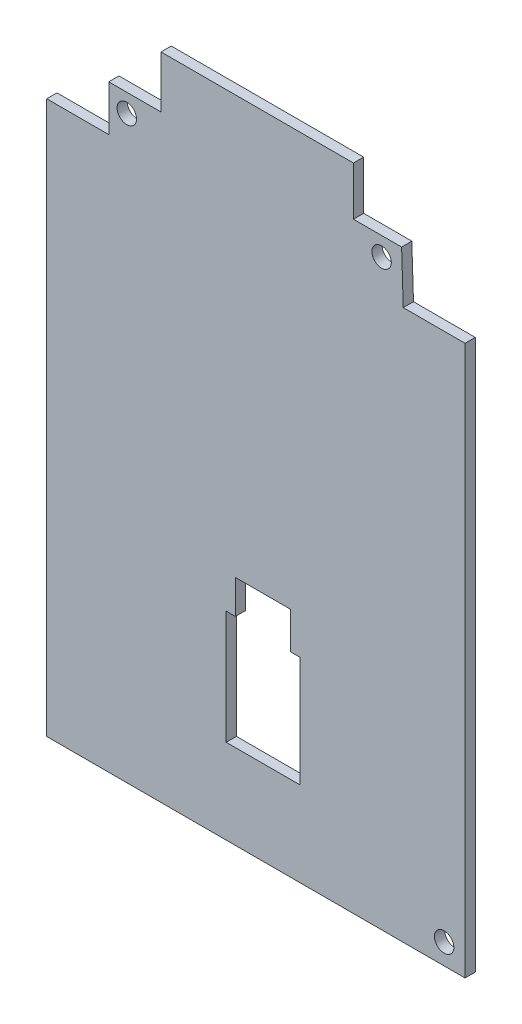
SolidWorks part; units mm, degrees
material "Petg 30% Infill"
ref_plane "Front Plane" through (0, 0, 0) normal (0, 0, 1) x (1, 0, 0)
ref_plane "Top Plane" through (0, 0, 0) normal (0, 1, 0) x (1, 0, 0)
ref_plane "Right Plane" through (0, 0, 0) normal (1, 0, 0) x (0, 0, -1)
sketch "Sketch6" plane through (0, 0, 0) normal (0, 0, 1) x (1, 0, 0)
  line L0 (501.7385, 124.7244) -> (807.8803, 124.7244)
  line L1 (807.8803, 124.7244) -> (807.8803, 34.0157)
  line L2 (807.8803, 34.0157) -> (501.7385, 34.0157)
  line L3 (501.7385, 34.0157) -> (501.7385, 124.7244)
  line L4 (28.3465, 566.9496) -> (813.5496, 566.9496)
  line L5 (813.5496, 566.9496) -> (813.5496, 28.3465)
  line L6 (813.5496, 28.3465) -> (28.3465, 28.3465)
  line L7 (28.3465, 28.3465) -> (28.3465, 566.9496)
  line L8 (34.0157, 561.2803) -> (807.8803, 561.2803)
  line L9 (807.8803, 561.2803) -> (807.8803, 34.0157)
  line L10 (807.8803, 34.0157) -> (34.0157, 34.0157)
  line L11 (34.0157, 34.0157) -> (34.0157, 561.2803)
  line L12 (170.0787, 561.2803) -> (170.0787, 566.9496)
  line L13 (311.811, 561.2803) -> (311.811, 566.9496)
  line L14 (453.5433, 561.2803) -> (453.5433, 566.9496)
  line L15 (595.2756, 561.2803) -> (595.2756, 566.9496)
  line L16 (737.0079, 561.2803) -> (737.0079, 566.9496)
  line L17 (102.3001, 562.4323) -> (100.1942, 562.4323)
  line L18 (101.247, 562.4323) -> (101.247, 566.1173)
  line L19 (101.247, 566.1173) -> (100.8961, 565.5909)
  line L20 (100.8961, 565.5909) -> (100.5452, 565.24)
  line L21 (100.5452, 565.24) -> (100.1942, 565.0645)
  line L22 (241.9265, 565.7664) -> (242.102, 565.9418)
  line L23 (242.102, 565.9418) -> (242.4529, 566.1173)
  line L24 (242.4529, 566.1173) -> (243.3302, 566.1173)
  line L25 (243.3302, 566.1173) -> (243.6815, 565.9418)
  line L26 (243.6815, 565.9418) -> (243.8569, 565.7664)
  line L27 (243.8569, 565.7664) -> (244.0324, 565.4155)
  line L28 (244.0324, 565.4155) -> (244.0324, 565.0645)
  line L29 (244.0324, 565.0645) -> (243.8569, 564.5381)
  line L30 (243.8569, 564.5381) -> (241.7511, 562.4323)
  line L31 (241.7511, 562.4323) -> (244.0324, 562.4323)
  line L32 (383.4833, 566.1173) -> (385.7647, 566.1173)
  line L33 (385.7647, 566.1173) -> (384.5362, 564.7136)
  line L34 (384.5362, 564.7136) -> (385.0626, 564.7136)
  line L35 (385.0626, 564.7136) -> (385.4137, 564.5381)
  line L36 (385.4137, 564.5381) -> (385.5892, 564.3624)
  line L37 (385.5892, 564.3624) -> (385.7647, 564.0115)
  line L38 (385.7647, 564.0115) -> (385.7647, 563.1341)
  line L39 (385.7647, 563.1341) -> (385.5892, 562.7832)
  line L40 (385.5892, 562.7832) -> (385.4137, 562.6077)
  line L41 (385.4137, 562.6077) -> (385.0626, 562.4323)
  line L42 (385.0626, 562.4323) -> (384.0097, 562.4323)
  line L43 (384.0097, 562.4323) -> (383.6588, 562.6077)
  line L44 (383.6588, 562.6077) -> (383.4833, 562.7832)
  line L45 (527.146, 564.8891) -> (527.146, 562.4323)
  line L46 (526.2684, 566.2928) -> (525.3911, 563.6605)
  line L47 (525.3911, 563.6605) -> (527.6724, 563.6605)
  line L48 (669.0538, 566.1173) -> (667.2989, 566.1173)
  line L49 (667.2989, 566.1173) -> (667.1234, 564.3624)
  line L50 (667.1234, 564.3624) -> (667.2989, 564.5381)
  line L51 (667.2989, 564.5381) -> (667.6498, 564.7136)
  line L52 (667.6498, 564.7136) -> (668.5271, 564.7136)
  line L53 (668.5271, 564.7136) -> (668.8783, 564.5381)
  line L54 (668.8783, 564.5381) -> (669.0538, 564.3624)
  line L55 (669.0538, 564.3624) -> (669.2293, 564.0115)
  line L56 (669.2293, 564.0115) -> (669.2293, 563.1341)
  line L57 (669.2293, 563.1341) -> (669.0538, 562.7832)
  line L58 (669.0538, 562.7832) -> (668.8783, 562.6077)
  line L59 (668.8783, 562.6077) -> (668.5271, 562.4323)
  line L60 (668.5271, 562.4323) -> (667.6498, 562.4323)
  line L61 (667.6498, 562.4323) -> (667.2989, 562.6077)
  line L62 (667.2989, 562.6077) -> (667.1234, 562.7832)
  line L63 (810.6106, 566.1173) -> (809.9085, 566.1173)
  line L64 (809.9085, 566.1173) -> (809.5575, 565.9418)
  line L65 (809.5575, 565.9418) -> (809.3821, 565.7664)
  line L66 (809.3821, 565.7664) -> (809.0311, 565.24)
  line L67 (809.0311, 565.24) -> (808.8557, 564.5381)
  line L68 (808.8557, 564.5381) -> (808.8557, 563.1341)
  line L69 (808.8557, 563.1341) -> (809.0311, 562.7832)
  line L70 (809.0311, 562.7832) -> (809.2066, 562.6077)
  line L71 (809.2066, 562.6077) -> (809.5575, 562.4323)
  line L72 (809.5575, 562.4323) -> (810.2594, 562.4323)
  line L73 (810.2594, 562.4323) -> (810.6106, 562.6077)
  line L74 (810.6106, 562.6077) -> (810.7861, 562.7832)
  line L75 (810.7861, 562.7832) -> (810.9615, 563.1341)
  line L76 (810.9615, 563.1341) -> (810.9615, 564.0115)
  line L77 (810.9615, 564.0115) -> (810.7861, 564.3624)
  line L78 (810.7861, 564.3624) -> (810.6106, 564.5381)
  line L79 (810.6106, 564.5381) -> (810.2594, 564.7136)
  line L80 (810.2594, 564.7136) -> (809.5575, 564.7136)
  line L81 (809.5575, 564.7136) -> (809.2066, 564.5381)
  line L82 (809.2066, 564.5381) -> (809.0311, 564.3624)
  line L83 (809.0311, 564.3624) -> (808.8557, 564.0115)
  line L84 (170.0787, 34.0157) -> (170.0787, 28.3465)
  line L85 (311.811, 34.0157) -> (311.811, 28.3465)
  line L86 (453.5433, 34.0157) -> (453.5433, 28.3465)
  line L87 (595.2756, 34.0157) -> (595.2756, 28.3465)
  line L88 (737.0079, 34.0157) -> (737.0079, 28.3465)
  line L89 (102.3001, 29.4985) -> (100.1942, 29.4985)
  line L90 (101.247, 29.4985) -> (101.247, 33.1835)
  line L91 (101.247, 33.1835) -> (100.8961, 32.6571)
  line L92 (100.8961, 32.6571) -> (100.5452, 32.3062)
  line L93 (100.5452, 32.3062) -> (100.1942, 32.1307)
  line L94 (241.9265, 32.8326) -> (242.102, 33.008)
  line L95 (242.102, 33.008) -> (242.4529, 33.1835)
  line L96 (242.4529, 33.1835) -> (243.3302, 33.1835)
  line L97 (243.3302, 33.1835) -> (243.6815, 33.008)
  line L98 (243.6815, 33.008) -> (243.8569, 32.8326)
  line L99 (243.8569, 32.8326) -> (244.0324, 32.4816)
  line L100 (244.0324, 32.4816) -> (244.0324, 32.1307)
  line L101 (244.0324, 32.1307) -> (243.8569, 31.6043)
  line L102 (243.8569, 31.6043) -> (241.7511, 29.4985)
  line L103 (241.7511, 29.4985) -> (244.0324, 29.4985)
  line L104 (383.4833, 33.1835) -> (385.7647, 33.1835)
  line L105 (385.7647, 33.1835) -> (384.5362, 31.7798)
  line L106 (384.5362, 31.7798) -> (385.0626, 31.7798)
  line L107 (385.0626, 31.7798) -> (385.4137, 31.6043)
  line L108 (385.4137, 31.6043) -> (385.5892, 31.4286)
  line L109 (385.5892, 31.4286) -> (385.7647, 31.0776)
  line L110 (385.7647, 31.0776) -> (385.7647, 30.2003)
  line L111 (385.7647, 30.2003) -> (385.5892, 29.8494)
  line L112 (385.5892, 29.8494) -> (385.4137, 29.6739)
  line L113 (385.4137, 29.6739) -> (385.0626, 29.4985)
  line L114 (385.0626, 29.4985) -> (384.0097, 29.4985)
  line L115 (384.0097, 29.4985) -> (383.6588, 29.6739)
  line L116 (383.6588, 29.6739) -> (383.4833, 29.8494)
  line L117 (527.146, 31.9552) -> (527.146, 29.4985)
  line L118 (526.2684, 33.3589) -> (525.3911, 30.7267)
  line L119 (525.3911, 30.7267) -> (527.6724, 30.7267)
  line L120 (669.0538, 33.1835) -> (667.2989, 33.1835)
  line L121 (667.2989, 33.1835) -> (667.1234, 31.4286)
  line L122 (667.1234, 31.4286) -> (667.2989, 31.6043)
  line L123 (667.2989, 31.6043) -> (667.6498, 31.7798)
  line L124 (667.6498, 31.7798) -> (668.5271, 31.7798)
  line L125 (668.5271, 31.7798) -> (668.8783, 31.6043)
  line L126 (668.8783, 31.6043) -> (669.0538, 31.4286)
  line L127 (669.0538, 31.4286) -> (669.2293, 31.0776)
  line L128 (669.2293, 31.0776) -> (669.2293, 30.2003)
  line L129 (669.2293, 30.2003) -> (669.0538, 29.8494)
  line L130 (669.0538, 29.8494) -> (668.8783, 29.6739)
  line L131 (668.8783, 29.6739) -> (668.5271, 29.4985)
  line L132 (668.5271, 29.4985) -> (667.6498, 29.4985)
  line L133 (667.6498, 29.4985) -> (667.2989, 29.6739)
  line L134 (667.2989, 29.6739) -> (667.1234, 29.8494)
  line L135 (810.6106, 33.1835) -> (809.9085, 33.1835)
  line L136 (809.9085, 33.1835) -> (809.5575, 33.008)
  line L137 (809.5575, 33.008) -> (809.3821, 32.8326)
  line L138 (809.3821, 32.8326) -> (809.0311, 32.3062)
  line L139 (809.0311, 32.3062) -> (808.8557, 31.6043)
  line L140 (808.8557, 31.6043) -> (808.8557, 30.2003)
  line L141 (808.8557, 30.2003) -> (809.0311, 29.8494)
  line L142 (809.0311, 29.8494) -> (809.2066, 29.6739)
  line L143 (809.2066, 29.6739) -> (809.5575, 29.4985)
  line L144 (809.5575, 29.4985) -> (810.2594, 29.4985)
  line L145 (810.2594, 29.4985) -> (810.6106, 29.6739)
  line L146 (810.6106, 29.6739) -> (810.7861, 29.8494)
  line L147 (810.7861, 29.8494) -> (810.9615, 30.2003)
  line L148 (810.9615, 30.2003) -> (810.9615, 31.0776)
  line L149 (810.9615, 31.0776) -> (810.7861, 31.4286)
  line L150 (810.7861, 31.4286) -> (810.6106, 31.6043)
  line L151 (810.6106, 31.6043) -> (810.2594, 31.7798)
  line L152 (810.2594, 31.7798) -> (809.5575, 31.7798)
  line L153 (809.5575, 31.7798) -> (809.2066, 31.6043)
  line L154 (809.2066, 31.6043) -> (809.0311, 31.4286)
  line L155 (809.0311, 31.4286) -> (808.8557, 31.0776)
  line L156 (28.3465, 425.2173) -> (34.0157, 425.2173)
  line L157 (28.3465, 283.485) -> (34.0157, 283.485)
  line L158 (28.3465, 141.7527) -> (34.0157, 141.7527)
  line L159 (30.3038, 495.4536) -> (32.0584, 495.4536)
  line L160 (29.9529, 494.4008) -> (31.1811, 498.0858)
  line L161 (31.1811, 498.0858) -> (32.4094, 494.4008)
  line L162 (31.4444, 354.5986) -> (31.9708, 354.4231)
  line L163 (31.9708, 354.4231) -> (32.1463, 354.2477)
  line L164 (32.1463, 354.2477) -> (32.3218, 353.8967)
  line L165 (32.3218, 353.8967) -> (32.3218, 353.3703)
  line L166 (32.3218, 353.3703) -> (32.1463, 353.0194)
  line L167 (32.1463, 353.0194) -> (31.9708, 352.844)
  line L168 (31.9708, 352.844) -> (31.6199, 352.6685)
  line L169 (31.6199, 352.6685) -> (30.2159, 352.6685)
  line L170 (30.2159, 352.6685) -> (30.2159, 356.3535)
  line L171 (30.2159, 356.3535) -> (31.4444, 356.3535)
  line L172 (31.4444, 356.3535) -> (31.7954, 356.1781)
  line L173 (31.7954, 356.1781) -> (31.9708, 356.0026)
  line L174 (31.9708, 356.0026) -> (32.1463, 355.6517)
  line L175 (32.1463, 355.6517) -> (32.1463, 355.3007)
  line L176 (32.1463, 355.3007) -> (31.9708, 354.9498)
  line L177 (31.9708, 354.9498) -> (31.7954, 354.7743)
  line L178 (31.7954, 354.7743) -> (31.4444, 354.5986)
  line L179 (31.4444, 354.5986) -> (30.2159, 354.5986)
  line L180 (32.3218, 211.2871) -> (32.1463, 211.1117)
  line L181 (32.1463, 211.1117) -> (31.6199, 210.9362)
  line L182 (31.6199, 210.9362) -> (31.269, 210.9362)
  line L183 (31.269, 210.9362) -> (30.7423, 211.1117)
  line L184 (30.7423, 211.1117) -> (30.3914, 211.4626)
  line L185 (30.3914, 211.4626) -> (30.2159, 211.8135)
  line L186 (30.2159, 211.8135) -> (30.0404, 212.5154)
  line L187 (30.0404, 212.5154) -> (30.0404, 213.0421)
  line L188 (30.0404, 213.0421) -> (30.2159, 213.7439)
  line L189 (30.2159, 213.7439) -> (30.3914, 214.0949)
  line L190 (30.3914, 214.0949) -> (30.7423, 214.4458)
  line L191 (30.7423, 214.4458) -> (31.269, 214.6213)
  line L192 (31.269, 214.6213) -> (31.6199, 214.6213)
  line L193 (31.6199, 214.6213) -> (32.1463, 214.4458)
  line L194 (32.1463, 214.4458) -> (32.3218, 214.2703)
  line L195 (30.2159, 69.2039) -> (30.2159, 72.889)
  line L196 (30.2159, 72.889) -> (31.0932, 72.889)
  line L197 (31.0932, 72.889) -> (31.6199, 72.7135)
  line L198 (31.6199, 72.7135) -> (31.9708, 72.3626)
  line L199 (31.9708, 72.3626) -> (32.1463, 72.0116)
  line L200 (32.1463, 72.0116) -> (32.3218, 71.3098)
  line L201 (32.3218, 71.3098) -> (32.3218, 70.7831)
  line L202 (32.3218, 70.7831) -> (32.1463, 70.0812)
  line L203 (32.1463, 70.0812) -> (31.9708, 69.7303)
  line L204 (31.9708, 69.7303) -> (31.6199, 69.3794)
  line L205 (31.6199, 69.3794) -> (31.0932, 69.2039)
  line L206 (31.0932, 69.2039) -> (30.2159, 69.2039)
  line L207 (813.5496, 425.2173) -> (807.8803, 425.2173)
  line L208 (813.5496, 283.485) -> (807.8803, 283.485)
  line L209 (813.5496, 141.7527) -> (807.8803, 141.7527)
  line L210 (809.8376, 495.4536) -> (811.5923, 495.4536)
  line L211 (809.4867, 494.4008) -> (810.7149, 498.0858)
  line L212 (810.7149, 498.0858) -> (811.9431, 494.4008)
  line L213 (810.9782, 354.5986) -> (811.5046, 354.4231)
  line L214 (811.5046, 354.4231) -> (811.6802, 354.2477)
  line L215 (811.6802, 354.2477) -> (811.8556, 353.8967)
  line L216 (811.8556, 353.8967) -> (811.8556, 353.3703)
  line L217 (811.8556, 353.3703) -> (811.6802, 353.0194)
  line L218 (811.6802, 353.0194) -> (811.5046, 352.844)
  line L219 (811.5046, 352.844) -> (811.1538, 352.6685)
  line L220 (811.1538, 352.6685) -> (809.7498, 352.6685)
  line L221 (809.7498, 352.6685) -> (809.7498, 356.3535)
  line L222 (809.7498, 356.3535) -> (810.9782, 356.3535)
  line L223 (810.9782, 356.3535) -> (811.3292, 356.1781)
  line L224 (811.3292, 356.1781) -> (811.5046, 356.0026)
  line L225 (811.5046, 356.0026) -> (811.6802, 355.6517)
  line L226 (811.6802, 355.6517) -> (811.6802, 355.3007)
  line L227 (811.6802, 355.3007) -> (811.5046, 354.9498)
  line L228 (811.5046, 354.9498) -> (811.3292, 354.7743)
  line L229 (811.3292, 354.7743) -> (810.9782, 354.5986)
  line L230 (810.9782, 354.5986) -> (809.7498, 354.5986)
  line L231 (811.8556, 211.2871) -> (811.6802, 211.1117)
  line L232 (811.6802, 211.1117) -> (811.1538, 210.9362)
  line L233 (811.1538, 210.9362) -> (810.8028, 210.9362)
  line L234 (810.8028, 210.9362) -> (810.2762, 211.1117)
  line L235 (810.2762, 211.1117) -> (809.9252, 211.4626)
  line L236 (809.9252, 211.4626) -> (809.7498, 211.8135)
  line L237 (809.7498, 211.8135) -> (809.5742, 212.5154)
  line L238 (809.5742, 212.5154) -> (809.5742, 213.0421)
  line L239 (809.5742, 213.0421) -> (809.7498, 213.7439)
  line L240 (809.7498, 213.7439) -> (809.9252, 214.0949)
  line L241 (809.9252, 214.0949) -> (810.2762, 214.4458)
  line L242 (810.2762, 214.4458) -> (810.8028, 214.6213)
  line L243 (810.8028, 214.6213) -> (811.1538, 214.6213)
  line L244 (811.1538, 214.6213) -> (811.6802, 214.4458)
  line L245 (811.6802, 214.4458) -> (811.8556, 214.2703)
  line L246 (809.7498, 69.2039) -> (809.7498, 72.889)
  line L247 (809.7498, 72.889) -> (810.627, 72.889)
  line L248 (810.627, 72.889) -> (811.1538, 72.7135)
  line L249 (811.1538, 72.7135) -> (811.5046, 72.3626)
  line L250 (811.5046, 72.3626) -> (811.6802, 72.0116)
  line L251 (811.6802, 72.0116) -> (811.8556, 71.3098)
  line L252 (811.8556, 71.3098) -> (811.8556, 70.7831)
  line L253 (811.8556, 70.7831) -> (811.6802, 70.0812)
  line L254 (811.6802, 70.0812) -> (811.5046, 69.7303)
  line L255 (811.5046, 69.7303) -> (811.1538, 69.3794)
  line L256 (811.1538, 69.3794) -> (810.627, 69.2039)
  line L257 (810.627, 69.2039) -> (809.7498, 69.2039)
  line L258 (568.2274, 45.9607) -> (568.2274, 50.2126)
  line L259 (568.2274, 50.2126) -> (569.24, 50.2126)
  line L260 (569.24, 50.2126) -> (569.8474, 50.0099)
  line L261 (569.8474, 50.0099) -> (570.2522, 49.6052)
  line L262 (570.2522, 49.6052) -> (570.4546, 49.2001)
  line L263 (570.4546, 49.2001) -> (570.6573, 48.3902)
  line L264 (570.6573, 48.3902) -> (570.6573, 47.7828)
  line L265 (570.6573, 47.7828) -> (570.4546, 46.9729)
  line L266 (570.4546, 46.9729) -> (570.2522, 46.5681)
  line L267 (570.2522, 46.5681) -> (569.8474, 46.1631)
  line L268 (569.8474, 46.1631) -> (569.24, 45.9607)
  line L269 (569.24, 45.9607) -> (568.2274, 45.9607)
  line L270 (574.3018, 45.9607) -> (574.3018, 48.1879)
  line L271 (574.3018, 48.1879) -> (574.0994, 48.5926)
  line L272 (574.0994, 48.5926) -> (573.6943, 48.7953)
  line L273 (573.6943, 48.7953) -> (572.8845, 48.7953)
  line L274 (572.8845, 48.7953) -> (572.4794, 48.5926)
  line L275 (574.3018, 46.1631) -> (573.8967, 45.9607)
  line L276 (573.8967, 45.9607) -> (572.8845, 45.9607)
  line L277 (572.8845, 45.9607) -> (572.4794, 46.1631)
  line L278 (572.4794, 46.1631) -> (572.277, 46.5681)
  line L279 (572.277, 46.5681) -> (572.277, 46.9729)
  line L280 (572.277, 46.9729) -> (572.4794, 47.378)
  line L281 (572.4794, 47.378) -> (572.8845, 47.5804)
  line L282 (572.8845, 47.5804) -> (573.8967, 47.5804)
  line L283 (573.8967, 47.5804) -> (574.3018, 47.7828)
  line L284 (575.7191, 48.7953) -> (577.3388, 48.7953)
  line L285 (576.3266, 50.2126) -> (576.3266, 46.5681)
  line L286 (576.3266, 46.5681) -> (576.529, 46.1631)
  line L287 (576.529, 46.1631) -> (576.934, 45.9607)
  line L288 (576.934, 45.9607) -> (577.3388, 45.9607)
  line L289 (580.3759, 46.1631) -> (579.9711, 45.9607)
  line L290 (579.9711, 45.9607) -> (579.1612, 45.9607)
  line L291 (579.1612, 45.9607) -> (578.7561, 46.1631)
  line L292 (578.7561, 46.1631) -> (578.5538, 46.5681)
  line L293 (578.5538, 46.5681) -> (578.5538, 48.1879)
  line L294 (578.5538, 48.1879) -> (578.7561, 48.5926)
  line L295 (578.7561, 48.5926) -> (579.1612, 48.7953)
  line L296 (579.1612, 48.7953) -> (579.9711, 48.7953)
  line L297 (579.9711, 48.7953) -> (580.3759, 48.5926)
  line L298 (580.3759, 48.5926) -> (580.5785, 48.1879)
  line L299 (580.5785, 48.1879) -> (580.5785, 47.7828)
  line L300 (580.5785, 47.7828) -> (578.5538, 47.378)
  line L301 (582.4006, 46.3655) -> (582.6033, 46.1631)
  line L302 (582.6033, 46.1631) -> (582.4006, 45.9607)
  line L303 (582.4006, 45.9607) -> (582.1982, 46.1631)
  line L304 (582.1982, 46.1631) -> (582.4006, 46.3655)
  line L305 (582.4006, 46.3655) -> (582.4006, 45.9607)
  line L306 (582.4006, 48.5926) -> (582.6033, 48.3902)
  line L307 (582.6033, 48.3902) -> (582.4006, 48.1879)
  line L308 (582.4006, 48.1879) -> (582.1982, 48.3902)
  line L309 (582.1982, 48.3902) -> (582.4006, 48.5926)
  line L310 (582.4006, 48.5926) -> (582.4006, 48.1879)
  line L311 (501.7385, 43.937) -> (807.8803, 43.937)
  line L312 (505.8652, 38.0236) -> (505.8652, 42.2756)
  line L313 (508.2951, 38.0236) -> (506.4727, 40.4532)
  line L314 (508.2951, 42.2756) -> (505.8652, 39.8458)
  line L315 (510.1172, 38.0236) -> (510.1172, 40.8583)
  line L316 (510.1172, 42.2756) -> (509.9148, 42.073)
  line L317 (509.9148, 42.073) -> (510.1172, 41.8705)
  line L318 (510.1172, 41.8705) -> (510.3198, 42.073)
  line L319 (510.3198, 42.073) -> (510.1172, 42.2756)
  line L320 (510.1172, 42.2756) -> (510.1172, 41.8705)
  line L321 (514.5718, 38.4284) -> (514.3691, 38.2261)
  line L322 (514.3691, 38.2261) -> (513.7617, 38.0236)
  line L323 (513.7617, 38.0236) -> (513.3569, 38.0236)
  line L324 (513.3569, 38.0236) -> (512.7494, 38.2261)
  line L325 (512.7494, 38.2261) -> (512.3444, 38.6311)
  line L326 (512.3444, 38.6311) -> (512.142, 39.0359)
  line L327 (512.142, 39.0359) -> (511.9396, 39.8458)
  line L328 (511.9396, 39.8458) -> (511.9396, 40.4532)
  line L329 (511.9396, 40.4532) -> (512.142, 41.2631)
  line L330 (512.142, 41.2631) -> (512.3444, 41.6682)
  line L331 (512.3444, 41.6682) -> (512.7494, 42.073)
  line L332 (512.7494, 42.073) -> (513.3569, 42.2756)
  line L333 (513.3569, 42.2756) -> (513.7617, 42.2756)
  line L334 (513.7617, 42.2756) -> (514.3691, 42.073)
  line L335 (514.3691, 42.073) -> (514.5718, 41.8705)
  line L336 (518.2163, 38.0236) -> (518.2163, 40.2508)
  line L337 (518.2163, 40.2508) -> (518.0136, 40.6556)
  line L338 (518.0136, 40.6556) -> (517.6089, 40.8583)
  line L339 (517.6089, 40.8583) -> (516.799, 40.8583)
  line L340 (516.799, 40.8583) -> (516.3939, 40.6556)
  line L341 (518.2163, 38.2261) -> (517.8113, 38.0236)
  line L342 (517.8113, 38.0236) -> (516.799, 38.0236)
  line L343 (516.799, 38.0236) -> (516.3939, 38.2261)
  line L344 (516.3939, 38.2261) -> (516.1916, 38.6311)
  line L345 (516.1916, 38.6311) -> (516.1916, 39.0359)
  line L346 (516.1916, 39.0359) -> (516.3939, 39.441)
  line L347 (516.3939, 39.441) -> (516.799, 39.6434)
  line L348 (516.799, 39.6434) -> (517.8113, 39.6434)
  line L349 (517.8113, 39.6434) -> (518.2163, 39.8458)
  line L350 (522.0632, 38.0236) -> (522.0632, 42.2756)
  line L351 (522.0632, 38.2261) -> (521.6584, 38.0236)
  line L352 (521.6584, 38.0236) -> (520.8483, 38.0236)
  line L353 (520.8483, 38.0236) -> (520.4435, 38.2261)
  line L354 (520.4435, 38.2261) -> (520.2411, 38.4284)
  line L355 (520.2411, 38.4284) -> (520.0384, 38.8335)
  line L356 (520.0384, 38.8335) -> (520.0384, 40.0485)
  line L357 (520.0384, 40.0485) -> (520.2411, 40.4532)
  line L358 (520.2411, 40.4532) -> (520.4435, 40.6556)
  line L359 (520.4435, 40.6556) -> (520.8483, 40.8583)
  line L360 (520.8483, 40.8583) -> (521.6584, 40.8583)
  line L361 (521.6584, 40.8583) -> (522.0632, 40.6556)
  line L362 (527.3277, 40.2508) -> (528.745, 40.2508)
  line L363 (529.3522, 38.0236) -> (527.3277, 38.0236)
  line L364 (527.3277, 38.0236) -> (527.3277, 42.2756)
  line L365 (527.3277, 42.2756) -> (529.3522, 42.2756)
  line L366 (531.1746, 38.4284) -> (531.377, 38.2261)
  line L367 (531.377, 38.2261) -> (531.1746, 38.0236)
  line L368 (531.1746, 38.0236) -> (530.9722, 38.2261)
  line L369 (530.9722, 38.2261) -> (531.1746, 38.4284)
  line L370 (531.1746, 38.4284) -> (531.1746, 38.0236)
  line L371 (533.1994, 38.0236) -> (533.1994, 42.2756)
  line L372 (533.1994, 42.2756) -> (534.2116, 42.2756)
  line L373 (534.2116, 42.2756) -> (534.8191, 42.073)
  line L374 (534.8191, 42.073) -> (535.2242, 41.6682)
  line L375 (535.2242, 41.6682) -> (535.4266, 41.2631)
  line L376 (535.4266, 41.2631) -> (535.629, 40.4532)
  line L377 (535.629, 40.4532) -> (535.629, 39.8458)
  line L378 (535.629, 39.8458) -> (535.4266, 39.0359)
  line L379 (535.4266, 39.0359) -> (535.2242, 38.6311)
  line L380 (535.2242, 38.6311) -> (534.8191, 38.2261)
  line L381 (534.8191, 38.2261) -> (534.2116, 38.0236)
  line L382 (534.2116, 38.0236) -> (533.1994, 38.0236)
  line L383 (537.4514, 38.4284) -> (537.6538, 38.2261)
  line L384 (537.6538, 38.2261) -> (537.4514, 38.0236)
  line L385 (537.4514, 38.0236) -> (537.249, 38.2261)
  line L386 (537.249, 38.2261) -> (537.4514, 38.4284)
  line L387 (537.4514, 38.4284) -> (537.4514, 38.0236)
  line L388 (539.2735, 39.2383) -> (541.2983, 39.2383)
  line L389 (538.8687, 38.0236) -> (540.286, 42.2756)
  line L390 (540.286, 42.2756) -> (541.7034, 38.0236)
  line L391 (543.1207, 38.4284) -> (543.3231, 38.2261)
  line L392 (543.3231, 38.2261) -> (543.1207, 38.0236)
  line L393 (543.1207, 38.0236) -> (542.9183, 38.2261)
  line L394 (542.9183, 38.2261) -> (543.1207, 38.4284)
  line L395 (543.1207, 38.4284) -> (543.1207, 38.0236)
  line L396 (548.9924, 40.4532) -> (548.5876, 40.6556)
  line L397 (548.5876, 40.6556) -> (548.3849, 40.8583)
  line L398 (548.3849, 40.8583) -> (548.1825, 41.2631)
  line L399 (548.1825, 41.2631) -> (548.1825, 41.4658)
  line L400 (548.1825, 41.4658) -> (548.3849, 41.8705)
  line L401 (548.3849, 41.8705) -> (548.5876, 42.073)
  line L402 (548.5876, 42.073) -> (548.9924, 42.2756)
  line L403 (548.9924, 42.2756) -> (549.8022, 42.2756)
  line L404 (549.8022, 42.2756) -> (550.2073, 42.073)
  line L405 (550.2073, 42.073) -> (550.4097, 41.8705)
  line L406 (550.4097, 41.8705) -> (550.6121, 41.4658)
  line L407 (550.6121, 41.4658) -> (550.6121, 41.2631)
  line L408 (550.6121, 41.2631) -> (550.4097, 40.8583)
  line L409 (550.4097, 40.8583) -> (550.2073, 40.6556)
  line L410 (550.2073, 40.6556) -> (549.8022, 40.4532)
  line L411 (549.8022, 40.4532) -> (548.9924, 40.4532)
  line L412 (548.9924, 40.4532) -> (548.5876, 40.2508)
  line L413 (548.5876, 40.2508) -> (548.3849, 40.0485)
  line L414 (548.3849, 40.0485) -> (548.1825, 39.6434)
  line L415 (548.1825, 39.6434) -> (548.1825, 38.8335)
  line L416 (548.1825, 38.8335) -> (548.3849, 38.4284)
  line L417 (548.3849, 38.4284) -> (548.5876, 38.2261)
  line L418 (548.5876, 38.2261) -> (548.9924, 38.0236)
  line L419 (548.9924, 38.0236) -> (549.8022, 38.0236)
  line L420 (549.8022, 38.0236) -> (550.2073, 38.2261)
  line L421 (550.2073, 38.2261) -> (550.4097, 38.4284)
  line L422 (550.4097, 38.4284) -> (550.6121, 38.8335)
  line L423 (550.6121, 38.8335) -> (550.6121, 39.6434)
  line L424 (550.6121, 39.6434) -> (550.4097, 40.0485)
  line L425 (550.4097, 40.0485) -> (550.2073, 40.2508)
  line L426 (550.2073, 40.2508) -> (549.8022, 40.4532)
  line L427 (552.4345, 38.4284) -> (552.6368, 38.2261)
  line L428 (552.6368, 38.2261) -> (552.4345, 38.0236)
  line L429 (552.4345, 38.0236) -> (552.2321, 38.2261)
  line L430 (552.2321, 38.2261) -> (552.4345, 38.4284)
  line L431 (552.4345, 38.4284) -> (552.4345, 38.0236)
  line L432 (555.2691, 42.2756) -> (555.6742, 42.2756)
  line L433 (555.6742, 42.2756) -> (556.079, 42.073)
  line L434 (556.079, 42.073) -> (556.2814, 41.8705)
  line L435 (556.2814, 41.8705) -> (556.484, 41.4658)
  line L436 (556.484, 41.4658) -> (556.6864, 40.6556)
  line L437 (556.6864, 40.6556) -> (556.6864, 39.6434)
  line L438 (556.6864, 39.6434) -> (556.484, 38.8335)
  line L439 (556.484, 38.8335) -> (556.2814, 38.4284)
  line L440 (556.2814, 38.4284) -> (556.079, 38.2261)
  line L441 (556.079, 38.2261) -> (555.6742, 38.0236)
  line L442 (555.6742, 38.0236) -> (555.2691, 38.0236)
  line L443 (555.2691, 38.0236) -> (554.864, 38.2261)
  line L444 (554.864, 38.2261) -> (554.6617, 38.4284)
  line L445 (554.6617, 38.4284) -> (554.4593, 38.8335)
  line L446 (554.4593, 38.8335) -> (554.2569, 39.6434)
  line L447 (554.2569, 39.6434) -> (554.2569, 40.6556)
  line L448 (554.2569, 40.6556) -> (554.4593, 41.4658)
  line L449 (554.4593, 41.4658) -> (554.6617, 41.8705)
  line L450 (554.6617, 41.8705) -> (554.864, 42.073)
  line L451 (554.864, 42.073) -> (555.2691, 42.2756)
  line L452 (558.5088, 38.4284) -> (558.7112, 38.2261)
  line L453 (558.7112, 38.2261) -> (558.5088, 38.0236)
  line L454 (558.5088, 38.0236) -> (558.3061, 38.2261)
  line L455 (558.3061, 38.2261) -> (558.5088, 38.4284)
  line L456 (558.5088, 38.4284) -> (558.5088, 38.0236)
  line L457 (562.3557, 40.8583) -> (562.3557, 38.0236)
  line L458 (561.3435, 42.478) -> (560.331, 39.441)
  line L459 (560.331, 39.441) -> (562.9632, 39.441)
  line L460 (501.7385, 52.4409) -> (807.8803, 52.4409)
  line L461 (749.5198, 45.9828) -> (748.1024, 48.0076)
  line L462 (747.0899, 45.9828) -> (747.0899, 50.2347)
  line L463 (747.0899, 50.2347) -> (748.7096, 50.2347)
  line L464 (748.7096, 50.2347) -> (749.1147, 50.0321)
  line L465 (749.1147, 50.0321) -> (749.3171, 49.8297)
  line L466 (749.3171, 49.8297) -> (749.5198, 49.4249)
  line L467 (749.5198, 49.4249) -> (749.5198, 48.8174)
  line L468 (749.5198, 48.8174) -> (749.3171, 48.4123)
  line L469 (749.3171, 48.4123) -> (749.1147, 48.21)
  line L470 (749.1147, 48.21) -> (748.7096, 48.0076)
  line L471 (748.7096, 48.0076) -> (747.0899, 48.0076)
  line L472 (752.9616, 46.1852) -> (752.5567, 45.9828)
  line L473 (752.5567, 45.9828) -> (751.7469, 45.9828)
  line L474 (751.7469, 45.9828) -> (751.3419, 46.1852)
  line L475 (751.3419, 46.1852) -> (751.1394, 46.5902)
  line L476 (751.1394, 46.5902) -> (751.1394, 48.21)
  line L477 (751.1394, 48.21) -> (751.3419, 48.6148)
  line L478 (751.3419, 48.6148) -> (751.7469, 48.8174)
  line L479 (751.7469, 48.8174) -> (752.5567, 48.8174)
  line L480 (752.5567, 48.8174) -> (752.9616, 48.6148)
  line L481 (752.9616, 48.6148) -> (753.1642, 48.21)
  line L482 (753.1642, 48.21) -> (753.1642, 47.8049)
  line L483 (753.1642, 47.8049) -> (751.1394, 47.4001)
  line L484 (754.5815, 48.8174) -> (755.5938, 45.9828)
  line L485 (755.5938, 45.9828) -> (756.6064, 48.8174)
  line L486 (758.226, 46.3876) -> (758.4285, 46.1852)
  line L487 (758.4285, 46.1852) -> (758.226, 45.9828)
  line L488 (758.226, 45.9828) -> (758.0237, 46.1852)
  line L489 (758.0237, 46.1852) -> (758.226, 46.3876)
  line L490 (758.226, 46.3876) -> (758.226, 45.9828)
  line L491 (758.226, 48.6148) -> (758.4285, 48.4123)
  line L492 (758.4285, 48.4123) -> (758.226, 48.21)
  line L493 (758.226, 48.21) -> (758.0237, 48.4123)
  line L494 (758.0237, 48.4123) -> (758.226, 48.6148)
  line L495 (758.226, 48.6148) -> (758.226, 48.21)
  line L496 (505.6628, 46.1631) -> (506.2703, 45.9607)
  line L497 (506.2703, 45.9607) -> (507.2825, 45.9607)
  line L498 (507.2825, 45.9607) -> (507.6876, 46.1631)
  line L499 (507.6876, 46.1631) -> (507.89, 46.3655)
  line L500 (507.89, 46.3655) -> (508.0924, 46.7705)
  line L501 (508.0924, 46.7705) -> (508.0924, 47.1753)
  line L502 (508.0924, 47.1753) -> (507.89, 47.5804)
  line L503 (507.89, 47.5804) -> (507.6876, 47.7828)
  line L504 (507.6876, 47.7828) -> (507.2825, 47.9855)
  line L505 (507.2825, 47.9855) -> (506.4727, 48.1879)
  line L506 (506.4727, 48.1879) -> (506.0679, 48.3902)
  line L507 (506.0679, 48.3902) -> (505.8652, 48.5926)
  line L508 (505.8652, 48.5926) -> (505.6628, 48.9977)
  line L509 (505.6628, 48.9977) -> (505.6628, 49.4028)
  line L510 (505.6628, 49.4028) -> (505.8652, 49.8076)
  line L511 (505.8652, 49.8076) -> (506.0679, 50.0099)
  line L512 (506.0679, 50.0099) -> (506.4727, 50.2126)
  line L513 (506.4727, 50.2126) -> (507.4852, 50.2126)
  line L514 (507.4852, 50.2126) -> (508.0924, 50.0099)
  line L515 (509.9148, 45.9607) -> (509.9148, 48.7953)
  line L516 (509.9148, 50.2126) -> (509.7124, 50.0099)
  line L517 (509.7124, 50.0099) -> (509.9148, 49.8076)
  line L518 (509.9148, 49.8076) -> (510.1172, 50.0099)
  line L519 (510.1172, 50.0099) -> (509.9148, 50.2126)
  line L520 (509.9148, 50.2126) -> (509.9148, 49.8076)
  line L521 (511.5345, 48.7953) -> (513.7617, 48.7953)
  line L522 (513.7617, 48.7953) -> (511.5345, 45.9607)
  line L523 (511.5345, 45.9607) -> (513.7617, 45.9607)
  line L524 (517.0014, 46.1631) -> (516.5963, 45.9607)
  line L525 (516.5963, 45.9607) -> (515.7864, 45.9607)
  line L526 (515.7864, 45.9607) -> (515.3817, 46.1631)
  line L527 (515.3817, 46.1631) -> (515.179, 46.5681)
  line L528 (515.179, 46.5681) -> (515.179, 48.1879)
  line L529 (515.179, 48.1879) -> (515.3817, 48.5926)
  line L530 (515.3817, 48.5926) -> (515.7864, 48.7953)
  line L531 (515.7864, 48.7953) -> (516.5963, 48.7953)
  line L532 (516.5963, 48.7953) -> (517.0014, 48.5926)
  line L533 (517.0014, 48.5926) -> (517.2038, 48.1879)
  line L534 (517.2038, 48.1879) -> (517.2038, 47.7828)
  line L535 (517.2038, 47.7828) -> (515.179, 47.378)
  line L536 (519.0262, 46.3655) -> (519.2286, 46.1631)
  line L537 (519.2286, 46.1631) -> (519.0262, 45.9607)
  line L538 (519.0262, 45.9607) -> (518.8238, 46.1631)
  line L539 (518.8238, 46.1631) -> (519.0262, 46.3655)
  line L540 (519.0262, 46.3655) -> (519.0262, 45.9607)
  line L541 (519.0262, 48.5926) -> (519.2286, 48.3902)
  line L542 (519.2286, 48.3902) -> (519.0262, 48.1879)
  line L543 (519.0262, 48.1879) -> (518.8238, 48.3902)
  line L544 (518.8238, 48.3902) -> (519.0262, 48.5926)
  line L545 (519.0262, 48.5926) -> (519.0262, 48.1879)
  line L546 (524.088, 47.1753) -> (526.1128, 47.1753)
  line L547 (523.6829, 45.9607) -> (525.1003, 50.2126)
  line L548 (525.1003, 50.2126) -> (526.5176, 45.9607)
  line L549 (529.7573, 48.7953) -> (529.7573, 45.9607)
  line L550 (528.745, 50.415) -> (527.7325, 47.378)
  line L551 (527.7325, 47.378) -> (530.3648, 47.378)
  line L552 (746.8101, 38.0236) -> (746.8101, 42.2756)
  line L553 (750.6572, 38.0236) -> (750.6572, 42.2756)
  line L554 (750.6572, 38.2261) -> (750.2522, 38.0236)
  line L555 (750.2522, 38.0236) -> (749.4423, 38.0236)
  line L556 (749.4423, 38.0236) -> (749.0373, 38.2261)
  line L557 (749.0373, 38.2261) -> (748.8349, 38.4284)
  line L558 (748.8349, 38.4284) -> (748.6325, 38.8335)
  line L559 (748.6325, 38.8335) -> (748.6325, 40.0485)
  line L560 (748.6325, 40.0485) -> (748.8349, 40.4532)
  line L561 (748.8349, 40.4532) -> (749.0373, 40.6556)
  line L562 (749.0373, 40.6556) -> (749.4423, 40.8583)
  line L563 (749.4423, 40.8583) -> (750.2522, 40.8583)
  line L564 (750.2522, 40.8583) -> (750.6572, 40.6556)
  line L565 (752.6821, 38.4284) -> (752.8844, 38.2261)
  line L566 (752.8844, 38.2261) -> (752.6821, 38.0236)
  line L567 (752.6821, 38.0236) -> (752.4794, 38.2261)
  line L568 (752.4794, 38.2261) -> (752.6821, 38.4284)
  line L569 (752.6821, 38.4284) -> (752.6821, 38.0236)
  line L570 (752.6821, 40.6556) -> (752.8844, 40.4532)
  line L571 (752.8844, 40.4532) -> (752.6821, 40.2508)
  line L572 (752.6821, 40.2508) -> (752.4794, 40.4532)
  line L573 (752.4794, 40.4532) -> (752.6821, 40.6556)
  line L574 (752.6821, 40.6556) -> (752.6821, 40.2508)
  line L575 (760.1735, 38.0236) -> (757.7439, 38.0236)
  line L576 (758.9586, 38.0236) -> (758.9586, 42.2756)
  line L577 (758.9586, 42.2756) -> (758.5537, 41.6682)
  line L578 (758.5537, 41.6682) -> (758.1487, 41.2631)
  line L579 (758.1487, 41.2631) -> (757.7439, 41.0607)
  line L580 (765.0329, 42.478) -> (761.3884, 37.0111)
  line L581 (768.6774, 38.0236) -> (766.2478, 38.0236)
  line L582 (767.4625, 38.0236) -> (767.4625, 42.2756)
  line L583 (767.4625, 42.2756) -> (767.0577, 41.6682)
  line L584 (767.0577, 41.6682) -> (766.6526, 41.2631)
  line L585 (766.6526, 41.2631) -> (766.2478, 41.0607)
  line L586 (501.7385, 63.7795) -> (807.8803, 63.7795)
  line L587 (506.5339, 61.7828) -> (509.7736, 61.7828)
  line L588 (507.4452, 56.1135) -> (508.1539, 61.7828)
  line L589 (510.9548, 56.1135) -> (511.4271, 59.893)
  line L590 (511.6635, 61.7828) -> (511.3596, 61.5127)
  line L591 (511.3596, 61.5127) -> (511.5957, 61.2428)
  line L592 (511.5957, 61.2428) -> (511.8996, 61.5127)
  line L593 (511.8996, 61.5127) -> (511.6635, 61.7828)
  line L594 (511.6635, 61.7828) -> (511.5957, 61.2428)
  line L595 (513.3169, 59.893) -> (515.4766, 59.893)
  line L596 (514.3629, 61.7828) -> (513.7554, 56.9234)
  line L597 (513.7554, 56.9234) -> (513.9581, 56.3834)
  line L598 (513.9581, 56.3834) -> (514.4641, 56.1135)
  line L599 (514.4641, 56.1135) -> (515.0041, 56.1135)
  line L600 (517.7038, 56.1135) -> (517.1975, 56.3834)
  line L601 (517.1975, 56.3834) -> (516.9952, 56.9234)
  line L602 (516.9952, 56.9234) -> (517.6026, 61.7828)
  line L603 (522.057, 56.3834) -> (521.4833, 56.1135)
  line L604 (521.4833, 56.1135) -> (520.4036, 56.1135)
  line L605 (520.4036, 56.1135) -> (519.8973, 56.3834)
  line L606 (519.8973, 56.3834) -> (519.6949, 56.9234)
  line L607 (519.6949, 56.9234) -> (519.9648, 59.0831)
  line L608 (519.9648, 59.0831) -> (520.3023, 59.6231)
  line L609 (520.3023, 59.6231) -> (520.8761, 59.893)
  line L610 (520.8761, 59.893) -> (521.9558, 59.893)
  line L611 (521.9558, 59.893) -> (522.4621, 59.6231)
  line L612 (522.4621, 59.6231) -> (522.6645, 59.0831)
  line L613 (522.6645, 59.0831) -> (522.597, 58.5431)
  line L614 (522.597, 58.5431) -> (519.8298, 58.0031)
  line L615 (524.7904, 56.6532) -> (525.0266, 56.3834)
  line L616 (525.0266, 56.3834) -> (524.723, 56.1135)
  line L617 (524.723, 56.1135) -> (524.4868, 56.3834)
  line L618 (524.4868, 56.3834) -> (524.7904, 56.6532)
  line L619 (524.7904, 56.6532) -> (524.723, 56.1135)
  line L620 (525.1618, 59.6231) -> (525.3979, 59.3529)
  line L621 (525.3979, 59.3529) -> (525.094, 59.0831)
  line L622 (525.094, 59.0831) -> (524.8579, 59.3529)
  line L623 (524.8579, 59.3529) -> (525.1618, 59.6231)
  line L624 (525.1618, 59.6231) -> (525.094, 59.0831)
  line L625 (507.2825, 69.1642) -> (505.8652, 69.1642)
  line L626 (505.8652, 66.9371) -> (505.8652, 71.189)
  line L627 (505.8652, 71.189) -> (507.89, 71.189)
  line L628 (509.5097, 66.9371) -> (509.5097, 69.7717)
  line L629 (509.5097, 71.189) -> (509.3073, 70.9863)
  line L630 (509.3073, 70.9863) -> (509.5097, 70.784)
  line L631 (509.5097, 70.784) -> (509.7124, 70.9863)
  line L632 (509.7124, 70.9863) -> (509.5097, 71.189)
  line L633 (509.5097, 71.189) -> (509.5097, 70.784)
  line L634 (512.142, 66.9371) -> (511.7372, 67.1394)
  line L635 (511.7372, 67.1394) -> (511.5345, 67.5445)
  line L636 (511.5345, 67.5445) -> (511.5345, 71.189)
  line L637 (515.3817, 67.1394) -> (514.9766, 66.9371)
  line L638 (514.9766, 66.9371) -> (514.1667, 66.9371)
  line L639 (514.1667, 66.9371) -> (513.7617, 67.1394)
  line L640 (513.7617, 67.1394) -> (513.5593, 67.5445)
  line L641 (513.5593, 67.5445) -> (513.5593, 69.1642)
  line L642 (513.5593, 69.1642) -> (513.7617, 69.569)
  line L643 (513.7617, 69.569) -> (514.1667, 69.7717)
  line L644 (514.1667, 69.7717) -> (514.9766, 69.7717)
  line L645 (514.9766, 69.7717) -> (515.3817, 69.569)
  line L646 (515.3817, 69.569) -> (515.5841, 69.1642)
  line L647 (515.5841, 69.1642) -> (515.5841, 68.7591)
  line L648 (515.5841, 68.7591) -> (513.5593, 68.3544)
  line L649 (517.4065, 67.3418) -> (517.6089, 67.1394)
  line L650 (517.6089, 67.1394) -> (517.4065, 66.9371)
  line L651 (517.4065, 66.9371) -> (517.2038, 67.1394)
  line L652 (517.2038, 67.1394) -> (517.4065, 67.3418)
  line L653 (517.4065, 67.3418) -> (517.4065, 66.9371)
  line L654 (517.4065, 69.569) -> (517.6089, 69.3666)
  line L655 (517.6089, 69.3666) -> (517.4065, 69.1642)
  line L656 (517.4065, 69.1642) -> (517.2038, 69.3666)
  line L657 (517.2038, 69.3666) -> (517.4065, 69.569)
  line L658 (517.4065, 69.569) -> (517.4065, 69.1642)
  line L659 (525.1003, 67.3418) -> (524.8979, 67.1394)
  line L660 (524.8979, 67.1394) -> (524.2904, 66.9371)
  line L661 (524.2904, 66.9371) -> (523.8856, 66.9371)
  line L662 (523.8856, 66.9371) -> (523.2782, 67.1394)
  line L663 (523.2782, 67.1394) -> (522.8731, 67.5445)
  line L664 (522.8731, 67.5445) -> (522.6707, 67.9493)
  line L665 (522.6707, 67.9493) -> (522.4683, 68.7591)
  line L666 (522.4683, 68.7591) -> (522.4683, 69.3666)
  line L667 (522.4683, 69.3666) -> (522.6707, 70.1765)
  line L668 (522.6707, 70.1765) -> (522.8731, 70.5815)
  line L669 (522.8731, 70.5815) -> (523.2782, 70.9863)
  line L670 (523.2782, 70.9863) -> (523.8856, 71.189)
  line L671 (523.8856, 71.189) -> (524.2904, 71.189)
  line L672 (524.2904, 71.189) -> (524.8979, 70.9863)
  line L673 (524.8979, 70.9863) -> (525.1003, 70.784)
  line L674 (526.9227, 66.9371) -> (526.9227, 71.189)
  line L675 (528.745, 66.9371) -> (528.745, 69.1642)
  line L676 (528.745, 69.1642) -> (528.5424, 69.569)
  line L677 (528.5424, 69.569) -> (528.1376, 69.7717)
  line L678 (528.1376, 69.7717) -> (527.5301, 69.7717)
  line L679 (527.5301, 69.7717) -> (527.125, 69.569)
  line L680 (527.125, 69.569) -> (526.9227, 69.3666)
  line L681 (532.5919, 66.9371) -> (532.5919, 69.1642)
  line L682 (532.5919, 69.1642) -> (532.3896, 69.569)
  line L683 (532.3896, 69.569) -> (531.9845, 69.7717)
  line L684 (531.9845, 69.7717) -> (531.1746, 69.7717)
  line L685 (531.1746, 69.7717) -> (530.7696, 69.569)
  line L686 (532.5919, 67.1394) -> (532.1869, 66.9371)
  line L687 (532.1869, 66.9371) -> (531.1746, 66.9371)
  line L688 (531.1746, 66.9371) -> (530.7696, 67.1394)
  line L689 (530.7696, 67.1394) -> (530.5672, 67.5445)
  line L690 (530.5672, 67.5445) -> (530.5672, 67.9493)
  line L691 (530.5672, 67.9493) -> (530.7696, 68.3544)
  line L692 (530.7696, 68.3544) -> (531.1746, 68.5568)
  line L693 (531.1746, 68.5568) -> (532.1869, 68.5568)
  line L694 (532.1869, 68.5568) -> (532.5919, 68.7591)
  line L695 (534.4143, 67.1394) -> (534.8191, 66.9371)
  line L696 (534.8191, 66.9371) -> (535.629, 66.9371)
  line L697 (535.629, 66.9371) -> (536.0341, 67.1394)
  line L698 (536.0341, 67.1394) -> (536.2365, 67.5445)
  line L699 (536.2365, 67.5445) -> (536.2365, 67.7469)
  line L700 (536.2365, 67.7469) -> (536.0341, 68.1517)
  line L701 (536.0341, 68.1517) -> (535.629, 68.3544)
  line L702 (535.629, 68.3544) -> (535.0215, 68.3544)
  line L703 (535.0215, 68.3544) -> (534.6168, 68.5568)
  line L704 (534.6168, 68.5568) -> (534.4143, 68.9618)
  line L705 (534.4143, 68.9618) -> (534.4143, 69.1642)
  line L706 (534.4143, 69.1642) -> (534.6168, 69.569)
  line L707 (534.6168, 69.569) -> (535.0215, 69.7717)
  line L708 (535.0215, 69.7717) -> (535.629, 69.7717)
  line L709 (535.629, 69.7717) -> (536.0341, 69.569)
  line L710 (537.8562, 67.1394) -> (538.2612, 66.9371)
  line L711 (538.2612, 66.9371) -> (539.0711, 66.9371)
  line L712 (539.0711, 66.9371) -> (539.4762, 67.1394)
  line L713 (539.4762, 67.1394) -> (539.6786, 67.5445)
  line L714 (539.6786, 67.5445) -> (539.6786, 67.7469)
  line L715 (539.6786, 67.7469) -> (539.4762, 68.1517)
  line L716 (539.4762, 68.1517) -> (539.0711, 68.3544)
  line L717 (539.0711, 68.3544) -> (538.4636, 68.3544)
  line L718 (538.4636, 68.3544) -> (538.0589, 68.5568)
  line L719 (538.0589, 68.5568) -> (537.8562, 68.9618)
  line L720 (537.8562, 68.9618) -> (537.8562, 69.1642)
  line L721 (537.8562, 69.1642) -> (538.0589, 69.569)
  line L722 (538.0589, 69.569) -> (538.4636, 69.7717)
  line L723 (538.4636, 69.7717) -> (539.0711, 69.7717)
  line L724 (539.0711, 69.7717) -> (539.4762, 69.569)
  line L725 (541.5009, 66.9371) -> (541.5009, 69.7717)
  line L726 (541.5009, 71.189) -> (541.2983, 70.9863)
  line L727 (541.2983, 70.9863) -> (541.5009, 70.784)
  line L728 (541.5009, 70.784) -> (541.7034, 70.9863)
  line L729 (541.7034, 70.9863) -> (541.5009, 71.189)
  line L730 (541.5009, 71.189) -> (541.5009, 70.784)
  line L731 (543.3231, 67.1394) -> (543.7281, 66.9371)
  line L732 (543.7281, 66.9371) -> (544.538, 66.9371)
  line L733 (544.538, 66.9371) -> (544.9428, 67.1394)
  line L734 (544.9428, 67.1394) -> (545.1455, 67.5445)
  line L735 (545.1455, 67.5445) -> (545.1455, 67.7469)
  line L736 (545.1455, 67.7469) -> (544.9428, 68.1517)
  line L737 (544.9428, 68.1517) -> (544.538, 68.3544)
  line L738 (544.538, 68.3544) -> (543.9305, 68.3544)
  line L739 (543.9305, 68.3544) -> (543.5255, 68.5568)
  line L740 (543.5255, 68.5568) -> (543.3231, 68.9618)
  line L741 (543.3231, 68.9618) -> (543.3231, 69.1642)
  line L742 (543.3231, 69.1642) -> (543.5255, 69.569)
  line L743 (543.5255, 69.569) -> (543.9305, 69.7717)
  line L744 (543.9305, 69.7717) -> (544.538, 69.7717)
  line L745 (544.538, 69.7717) -> (544.9428, 69.569)
  line L746 (546.9676, 67.3418) -> (547.1702, 67.1394)
  line L747 (547.1702, 67.1394) -> (546.9676, 66.9371)
  line L748 (546.9676, 66.9371) -> (546.7652, 67.1394)
  line L749 (546.7652, 67.1394) -> (546.9676, 67.3418)
  line L750 (546.9676, 67.3418) -> (546.9676, 66.9371)
  line L751 (548.9924, 66.9371) -> (548.9924, 71.189)
  line L752 (549.3974, 68.5568) -> (550.6121, 66.9371)
  line L753 (550.6121, 69.7717) -> (548.9924, 68.1517)
  line L754 (552.4345, 66.9371) -> (552.4345, 69.7717)
  line L755 (552.4345, 71.189) -> (552.2321, 70.9863)
  line L756 (552.2321, 70.9863) -> (552.4345, 70.784)
  line L757 (552.4345, 70.784) -> (552.6368, 70.9863)
  line L758 (552.6368, 70.9863) -> (552.4345, 71.189)
  line L759 (552.4345, 71.189) -> (552.4345, 70.784)
  line L760 (556.2814, 67.1394) -> (555.8766, 66.9371)
  line L761 (555.8766, 66.9371) -> (555.0667, 66.9371)
  line L762 (555.0667, 66.9371) -> (554.6617, 67.1394)
  line L763 (554.6617, 67.1394) -> (554.4593, 67.3418)
  line L764 (554.4593, 67.3418) -> (554.2569, 67.7469)
  line L765 (554.2569, 67.7469) -> (554.2569, 68.9618)
  line L766 (554.2569, 68.9618) -> (554.4593, 69.3666)
  line L767 (554.4593, 69.3666) -> (554.6617, 69.569)
  line L768 (554.6617, 69.569) -> (555.0667, 69.7717)
  line L769 (555.0667, 69.7717) -> (555.8766, 69.7717)
  line L770 (555.8766, 69.7717) -> (556.2814, 69.569)
  line L771 (559.9261, 66.9371) -> (559.9261, 69.1642)
  line L772 (559.9261, 69.1642) -> (559.7235, 69.569)
  line L773 (559.7235, 69.569) -> (559.3187, 69.7717)
  line L774 (559.3187, 69.7717) -> (558.5088, 69.7717)
  line L775 (558.5088, 69.7717) -> (558.1038, 69.569)
  line L776 (559.9261, 67.1394) -> (559.5211, 66.9371)
  line L777 (559.5211, 66.9371) -> (558.5088, 66.9371)
  line L778 (558.5088, 66.9371) -> (558.1038, 67.1394)
  line L779 (558.1038, 67.1394) -> (557.9014, 67.5445)
  line L780 (557.9014, 67.5445) -> (557.9014, 67.9493)
  line L781 (557.9014, 67.9493) -> (558.1038, 68.3544)
  line L782 (558.1038, 68.3544) -> (558.5088, 68.5568)
  line L783 (558.5088, 68.5568) -> (559.5211, 68.5568)
  line L784 (559.5211, 68.5568) -> (559.9261, 68.7591)
  line L785 (563.773, 66.9371) -> (563.773, 71.189)
  line L786 (563.773, 67.1394) -> (563.368, 66.9371)
  line L787 (563.368, 66.9371) -> (562.5581, 66.9371)
  line L788 (562.5581, 66.9371) -> (562.1533, 67.1394)
  line L789 (562.1533, 67.1394) -> (561.9507, 67.3418)
  line L790 (561.9507, 67.3418) -> (561.7483, 67.7469)
  line L791 (561.7483, 67.7469) -> (561.7483, 68.9618)
  line L792 (561.7483, 68.9618) -> (561.9507, 69.3666)
  line L793 (561.9507, 69.3666) -> (562.1533, 69.569)
  line L794 (562.1533, 69.569) -> (562.5581, 69.7717)
  line L795 (562.5581, 69.7717) -> (563.368, 69.7717)
  line L796 (563.368, 69.7717) -> (563.773, 69.569)
  line L797 (564.7853, 66.532) -> (568.025, 66.532)
  line L798 (569.0373, 69.7717) -> (569.0373, 65.5197)
  line L799 (569.0373, 69.569) -> (569.4423, 69.7717)
  line L800 (569.4423, 69.7717) -> (570.2522, 69.7717)
  line L801 (570.2522, 69.7717) -> (570.6573, 69.569)
  line L802 (570.6573, 69.569) -> (570.8597, 69.3666)
  line L803 (570.8597, 69.3666) -> (571.062, 68.9618)
  line L804 (571.062, 68.9618) -> (571.062, 67.7469)
  line L805 (571.062, 67.7469) -> (570.8597, 67.3418)
  line L806 (570.8597, 67.3418) -> (570.6573, 67.1394)
  line L807 (570.6573, 67.1394) -> (570.2522, 66.9371)
  line L808 (570.2522, 66.9371) -> (569.4423, 66.9371)
  line L809 (569.4423, 66.9371) -> (569.0373, 67.1394)
  line L810 (574.7066, 67.1394) -> (574.3018, 66.9371)
  line L811 (574.3018, 66.9371) -> (573.4919, 66.9371)
  line L812 (573.4919, 66.9371) -> (573.0869, 67.1394)
  line L813 (573.0869, 67.1394) -> (572.8845, 67.3418)
  line L814 (572.8845, 67.3418) -> (572.682, 67.7469)
  line L815 (572.682, 67.7469) -> (572.682, 68.9618)
  line L816 (572.682, 68.9618) -> (572.8845, 69.3666)
  line L817 (572.8845, 69.3666) -> (573.0869, 69.569)
  line L818 (573.0869, 69.569) -> (573.4919, 69.7717)
  line L819 (573.4919, 69.7717) -> (574.3018, 69.7717)
  line L820 (574.3018, 69.7717) -> (574.7066, 69.569)
  line L821 (576.529, 66.9371) -> (576.529, 71.189)
  line L822 (576.529, 69.569) -> (576.934, 69.7717)
  line L823 (576.934, 69.7717) -> (577.7439, 69.7717)
  line L824 (577.7439, 69.7717) -> (578.1487, 69.569)
  line L825 (578.1487, 69.569) -> (578.3513, 69.3666)
  line L826 (578.3513, 69.3666) -> (578.5538, 68.9618)
  line L827 (578.5538, 68.9618) -> (578.5538, 67.7469)
  line L828 (578.5538, 67.7469) -> (578.3513, 67.3418)
  line L829 (578.3513, 67.3418) -> (578.1487, 67.1394)
  line L830 (578.1487, 67.1394) -> (577.7439, 66.9371)
  line L831 (577.7439, 66.9371) -> (576.934, 66.9371)
  line L832 (576.934, 66.9371) -> (576.529, 67.1394)
  line L833 (501.7385, 80.7874) -> (807.8803, 80.7874)
  line L834 (505.6628, 74.793) -> (506.2703, 74.5906)
  line L835 (506.2703, 74.5906) -> (507.2825, 74.5906)
  line L836 (507.2825, 74.5906) -> (507.6876, 74.793)
  line L837 (507.6876, 74.793) -> (507.89, 74.9954)
  line L838 (507.89, 74.9954) -> (508.0924, 75.4005)
  line L839 (508.0924, 75.4005) -> (508.0924, 75.8052)
  line L840 (508.0924, 75.8052) -> (507.89, 76.2103)
  line L841 (507.89, 76.2103) -> (507.6876, 76.4127)
  line L842 (507.6876, 76.4127) -> (507.2825, 76.6154)
  line L843 (507.2825, 76.6154) -> (506.4727, 76.8178)
  line L844 (506.4727, 76.8178) -> (506.0679, 77.0202)
  line L845 (506.0679, 77.0202) -> (505.8652, 77.2226)
  line L846 (505.8652, 77.2226) -> (505.6628, 77.6276)
  line L847 (505.6628, 77.6276) -> (505.6628, 78.0327)
  line L848 (505.6628, 78.0327) -> (505.8652, 78.4375)
  line L849 (505.8652, 78.4375) -> (506.0679, 78.6399)
  line L850 (506.0679, 78.6399) -> (506.4727, 78.8426)
  line L851 (506.4727, 78.8426) -> (507.4852, 78.8426)
  line L852 (507.4852, 78.8426) -> (508.0924, 78.6399)
  line L853 (509.9148, 74.5906) -> (509.9148, 78.8426)
  line L854 (511.7372, 74.5906) -> (511.7372, 76.8178)
  line L855 (511.7372, 76.8178) -> (511.5345, 77.2226)
  line L856 (511.5345, 77.2226) -> (511.1297, 77.4252)
  line L857 (511.1297, 77.4252) -> (510.5223, 77.4252)
  line L858 (510.5223, 77.4252) -> (510.1172, 77.2226)
  line L859 (510.1172, 77.2226) -> (509.9148, 77.0202)
  line L860 (515.3817, 74.793) -> (514.9766, 74.5906)
  line L861 (514.9766, 74.5906) -> (514.1667, 74.5906)
  line L862 (514.1667, 74.5906) -> (513.7617, 74.793)
  line L863 (513.7617, 74.793) -> (513.5593, 75.198)
  line L864 (513.5593, 75.198) -> (513.5593, 76.8178)
  line L865 (513.5593, 76.8178) -> (513.7617, 77.2226)
  line L866 (513.7617, 77.2226) -> (514.1667, 77.4252)
  line L867 (514.1667, 77.4252) -> (514.9766, 77.4252)
  line L868 (514.9766, 77.4252) -> (515.3817, 77.2226)
  line L869 (515.3817, 77.2226) -> (515.5841, 76.8178)
  line L870 (515.5841, 76.8178) -> (515.5841, 76.4127)
  line L871 (515.5841, 76.4127) -> (513.5593, 76.0079)
  line L872 (519.0262, 74.793) -> (518.6211, 74.5906)
  line L873 (518.6211, 74.5906) -> (517.8113, 74.5906)
  line L874 (517.8113, 74.5906) -> (517.4065, 74.793)
  line L875 (517.4065, 74.793) -> (517.2038, 75.198)
  line L876 (517.2038, 75.198) -> (517.2038, 76.8178)
  line L877 (517.2038, 76.8178) -> (517.4065, 77.2226)
  line L878 (517.4065, 77.2226) -> (517.8113, 77.4252)
  line L879 (517.8113, 77.4252) -> (518.6211, 77.4252)
  line L880 (518.6211, 77.4252) -> (519.0262, 77.2226)
  line L881 (519.0262, 77.2226) -> (519.2286, 76.8178)
  line L882 (519.2286, 76.8178) -> (519.2286, 76.4127)
  line L883 (519.2286, 76.4127) -> (517.2038, 76.0079)
  line L884 (520.4435, 77.4252) -> (522.0632, 77.4252)
  line L885 (521.051, 78.8426) -> (521.051, 75.198)
  line L886 (521.051, 75.198) -> (521.2534, 74.793)
  line L887 (521.2534, 74.793) -> (521.6584, 74.5906)
  line L888 (521.6584, 74.5906) -> (522.0632, 74.5906)
  line L889 (523.4806, 74.9954) -> (523.6829, 74.793)
  line L890 (523.6829, 74.793) -> (523.4806, 74.5906)
  line L891 (523.4806, 74.5906) -> (523.2782, 74.793)
  line L892 (523.2782, 74.793) -> (523.4806, 74.9954)
  line L893 (523.4806, 74.9954) -> (523.4806, 74.5906)
  line L894 (523.4806, 77.2226) -> (523.6829, 77.0202)
  line L895 (523.6829, 77.0202) -> (523.4806, 76.8178)
  line L896 (523.4806, 76.8178) -> (523.2782, 77.0202)
  line L897 (523.2782, 77.0202) -> (523.4806, 77.2226)
  line L898 (523.4806, 77.2226) -> (523.4806, 76.8178)
  line L899 (558.4314, 52.4409) -> (558.4314, 43.937)
  line L900 (739.8488, 52.4409) -> (739.8488, 34.0157)
  line L901 (352.8, 274.896) -> (320.4, 274.896)
  line L902 (320.4, 255.096) -> (315, 255.096)
  line L903 (389.1969, 516.096) -> (389.1969, 496.296)
  line L904 (352.8, 253.296) -> (352.8, 274.896)
  line L905 (358.2, 253.296) -> (352.8, 253.296)
  line L906 (315, 255.096) -> (315, 188.496)
  line L907 (276.5197, 494.8929) -> (276.5197, 514.6929)
  line L908 (245.9197, 467.8929) -> (245.9197, 484.0929)
  line L909 (240.5197, 462.4929) -> (215.3197, 462.4929)
  line L910 (320.4, 274.896) -> (320.4, 255.096)
  line L911 (423.2358, 461.5472) -> (450, 461.4582)
  line L912 (315, 188.496) -> (358.2, 188.496)
  line L913 (209.9197, 457.0929) -> (210.5572, 145.296)
  line L914 (358.2, 188.496) -> (358.2, 253.296)
  line L915 (454.7622, 456.696) -> (454.7622, 143.496)
  line L916 (251.3197, 489.4929) -> (271.1197, 489.4929)
  line L917 (385.2, 520.0929) -> (281.9197, 520.0929)
  line L918 (215.3197, 139.896) -> (450, 138.7338)
  line L919 (417.9765, 485.9816) -> (417.9765, 467.9816)
  line L920 (394.2, 491.2929) -> (412.2, 491.2929)
  circle A0 centre (406.1197, 480.4929) radius 5.692
  circle A1 centre (256.7197, 478.6929) radius 5.692
  circle A2 centre (442.8, 150.988) radius 5.692
  spline S0 degree 3 poles (389.1969, 516.096) (389.1969, 518.3034) (387.4074, 520.0929) (385.2, 520.0929) knots 0 0 0 0 2 2 2 2
  spline S1 degree 3 poles (240.5197, 462.4929) (243.502, 462.4929) (245.9197, 464.9105) (245.9197, 467.8929) knots 0 0 0 0 1 1 1 1
  spline S2 degree 3 poles (271.1197, 489.4929) (274.102, 489.4929) (276.5197, 491.9105) (276.5197, 494.8929) knots 0 0 0 0 1 1 1 1
  spline S3 degree 2 poles (276.5197, 494.8929) (276.5197, 494.8929) (276.5197, 494.8929) knots 1 1 1 2 2 2
  spline S4 degree 3 poles (417.9765, 485.9816) (417.7241, 488.9843) (415.2133, 491.2929) (412.2, 491.2929) knots 0 0 0 0 1 1 1 1
  spline S5 degree 3 poles (454.7622, 456.696) (454.7622, 459.3261) (452.6301, 461.4582) (450, 461.4582) knots 0 0 0 0 1 1 1 1
  spline S6 degree 3 poles (215.3197, 462.4929) (212.3374, 462.4929) (209.9197, 460.0752) (209.9197, 457.0929) knots 0 0 0 0 2 2 2 2
  spline S7 degree 3 poles (389.1969, 496.296) (389.1969, 493.5329) (391.4369, 491.2929) (394.2, 491.2929) knots 0 0 0 0 1 1 1 1
  spline S8 degree 3 poles (281.9197, 520.0929) (278.9374, 520.0929) (276.5197, 517.6752) (276.5197, 514.6929) knots 0 0 0 0 1 1 1 1
  spline S9 degree 3 poles (210.5572, 145.296) (210.5573, 142.5531) (212.5983, 140.2388) (215.3197, 139.896) knots 0 0 0 0 1 1 1 1
  spline S10 degree 3 poles (251.3197, 489.4929) (248.3374, 489.4929) (245.9197, 487.0752) (245.9197, 484.0929) knots 0 0 0 0 1 1 1 1
  spline S11 degree 3 poles (450, 138.7338) (452.6301, 138.7338) (454.7622, 140.8659) (454.7622, 143.496) knots 0 0 0 0 2 2 2 2
  spline S12 degree 3 poles (417.9767, 467.9816) (417.7683, 464.7886) (420.0653, 461.9784) (423.2358, 461.5472) knots 0 0 0 0 1 1 1 1
  text T0 "1" font "SWTXT" height 0.2
  text T1 "2" font "SWTXT" height 0.2
  text T2 "3" font "SWTXT" height 0.2
  text T3 "4" font "SWTXT" height 0.2
  text T4 "5" font "SWTXT" height 0.2
  text T5 "6" font "SWTXT" height 0.2
  text T6 "1" font "SWTXT" height 0.2
  text T7 "2" font "SWTXT" height 0.2
  text T8 "3" font "SWTXT" height 0.2
  text T9 "4" font "SWTXT" height 0.2
  text T10 "5" font "SWTXT" height 0.2
  text T11 "6" font "SWTXT" height 0.2
  text T12 "A" font "SWTXT" height 0.2
  text T13 "B" font "SWTXT" height 0.2
  text T14 "C" font "SWTXT" height 0.2
  text T15 "D" font "SWTXT" height 0.2
  text T16 "A" font "SWTXT" height 0.2
  text T17 "B" font "SWTXT" height 0.2
  text T18 "C" font "SWTXT" height 0.2
  text T19 "D" font "SWTXT" height 0.2
  text T20 "Date:" font "SWTXT" height 0.2
  text T21 "KiCad E.D.A. 8.0.4" font "SWTXT" height 0.2
  text T22 "Rev:" font "SWTXT" height 0.2
  text T23 "Size: A4" font "SWTXT" height 0.2
  text T24 "Id: 1/1" font "SWTXT" height 0.2
  text T25 "Title:" font "SWTXT" height 0.2
  text T26 "File: Chassis.kicad_pcb" font "SWTXT" height 0.2
  text T27 "Sheet:" font "SWTXT" height 0.2
sketch "Sketch8" plane through (0, 0, 0) normal (0, 0, 1) x (1, 0, 0)
  line L0 (455.0461, 138.8153) -> (455.0461, 461.1401)
  line L1 (455.0461, 461.1401) -> (418.8188, 461.1401)
  line L2 (418.8188, 461.1401) -> (417.8545, 491.4247)
  line L3 (417.8545, 491.4247) -> (389.6232, 491.4247)
  line L4 (389.6232, 491.4247) -> (389.6232, 519.9661)
  line L5 (389.6232, 519.9661) -> (276.7788, 519.9661)
  line L6 (276.7788, 519.9661) -> (276.7788, 489.4533)
  line L7 (276.7788, 489.4533) -> (246.1389, 489.4533)
  line L8 (246.1389, 489.4533) -> (246.1389, 462.6651)
  line L9 (246.1389, 462.6651) -> (209.773, 462.6651)
  line L10 (209.773, 462.6651) -> (209.773, 138.8153)
  line L11 (209.773, 138.8153) -> (455.0461, 138.8153)
  line L13 (352.8, 274.896) -> (320.4, 274.896)
  line L14 (320.4, 274.896) -> (320.4, 255.096)
  line L15 (320.4, 255.096) -> (315, 255.096)
  line L16 (315, 255.096) -> (315, 188.496)
  line L17 (315, 188.496) -> (358.2, 188.496)
  line L18 (358.2, 188.496) -> (358.2, 253.296)
  line L19 (358.2, 253.296) -> (352.8, 253.296)
  line L20 (352.8, 253.296) -> (352.8, 274.896)
  dimension "D1" = 323.8498
extrude "Boss-Extrude1" add sketch "Sketch8" along normal blind 6
sketch "Sketch9" plane through (0, 0, 0) normal (0, 0, -1) x (-1, 0, 0)
  circle A0 centre (-442.8, 150.988) radius 5.692
  circle A1 centre (-256.7197, 478.6929) radius 5.692
  circle A2 centre (-406.1197, 480.4929) radius 5.692
extrude "Cut-Extrude1" cut sketch "Sketch9" against normal blind 6
scale "Scale2" scale about centroid uniform scaling yes scale factor 0.3527
